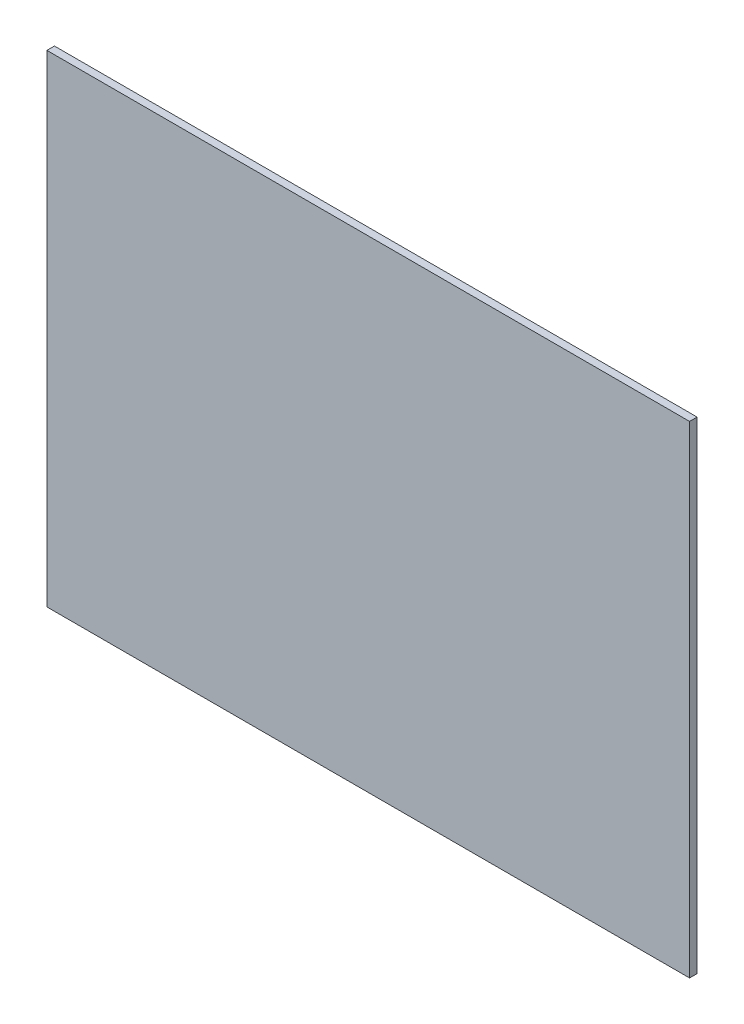
SolidWorks part; units mm, degrees
ref_plane "Front Plane" through (0, 0, 0) normal (0, 0, 1) x (1, 0, 0)
ref_plane "Top Plane" through (0, 0, 0) normal (0, 1, 0) x (1, 0, 0)
ref_plane "Right Plane" through (0, 0, 0) normal (1, 0, 0) x (0, 0, -1)
sketch "Sketch1" plane through (0, 0, 0) normal (0, 0, 1) x (1, 0, 0)
  line L1 (0, 304.8) -> (406.4, 304.8)
  line L2 (0, 304.8) -> (0, 0)
  line L3 (0, 0) -> (406.4, 0)
  line L4 (406.4, 304.8) -> (406.4, 0)
  point P4 (0, 0)
  dimension "D1" = 304.8
  dimension "D2" = 406.4
extrude "Boss-Extrude1" add sketch "Sketch1" along normal blind 4.7625
